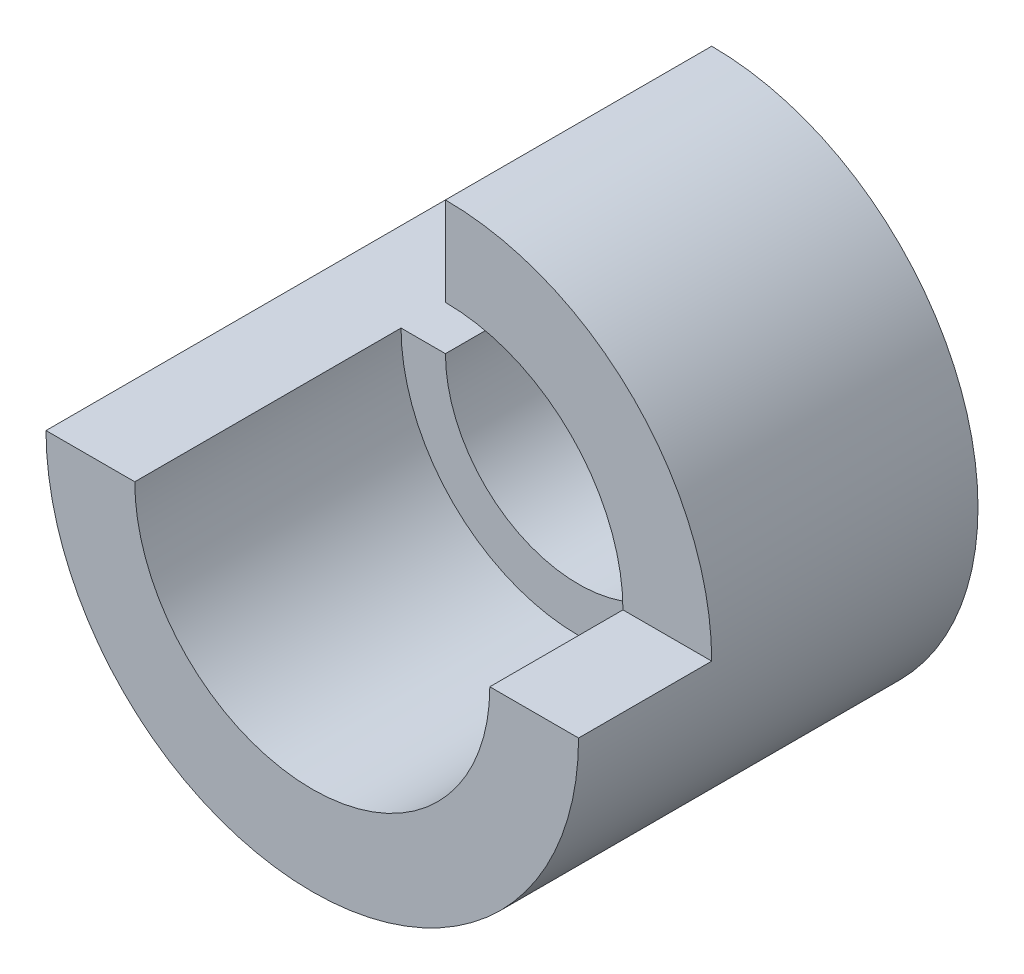
SolidWorks part; units mm, degrees
ref_plane "Front" through (0, 0, 0) normal (0, 0, 1) x (1, 0, 0)
ref_plane "Top" through (0, 0, 0) normal (0, 1, 0) x (1, 0, 0)
ref_plane "Right" through (0, 0, 0) normal (1, 0, 0) x (0, 0, -1)
sketch "Sketch1" plane through (0, 0, 0) normal (0, 0, 1) x (1, 0, 0)
  line L0 (-6, 0) -> (-3, 0)
  line L1 (0, 3) -> (0, 6)
  arc A0 (-6, 0) -> (0, 6) centre (0, 0) ccw
  arc A1 (-3, 0) -> (0, 3) centre (0, 0) ccw
  dimension "D1" = 6
  dimension "D2" = 12
extrude "Boss-Extrude1" add sketch "Sketch1" along normal blind 9
sketch "Sketch2" plane through (0, 0, 9) normal (0, 0, 1) x (1, 0, 0)
  line L0 (0, 6) -> (0, 3) construction
  line L1 (6, 0) -> (0, 0)
  line L2 (6, 0) -> (6, 6)
  line L3 (6, 6) -> (0, 6)
  line L4 (0, 0) -> (0, 6)
  arc A0 (-6, 0) -> (0, 6) centre (0, 0) ccw construction
extrude "Cut-Extrude1" cut sketch "Sketch2" against normal blind 3
sketch "Sketch3" plane through (0, 0, 9) normal (0, 0, 1) x (1, 0, 0)
  circle A0 centre (0, 0) radius 4
  dimension "D1" = 8
extrude "Cut-Extrude2" cut sketch "Sketch3" against normal blind 6
